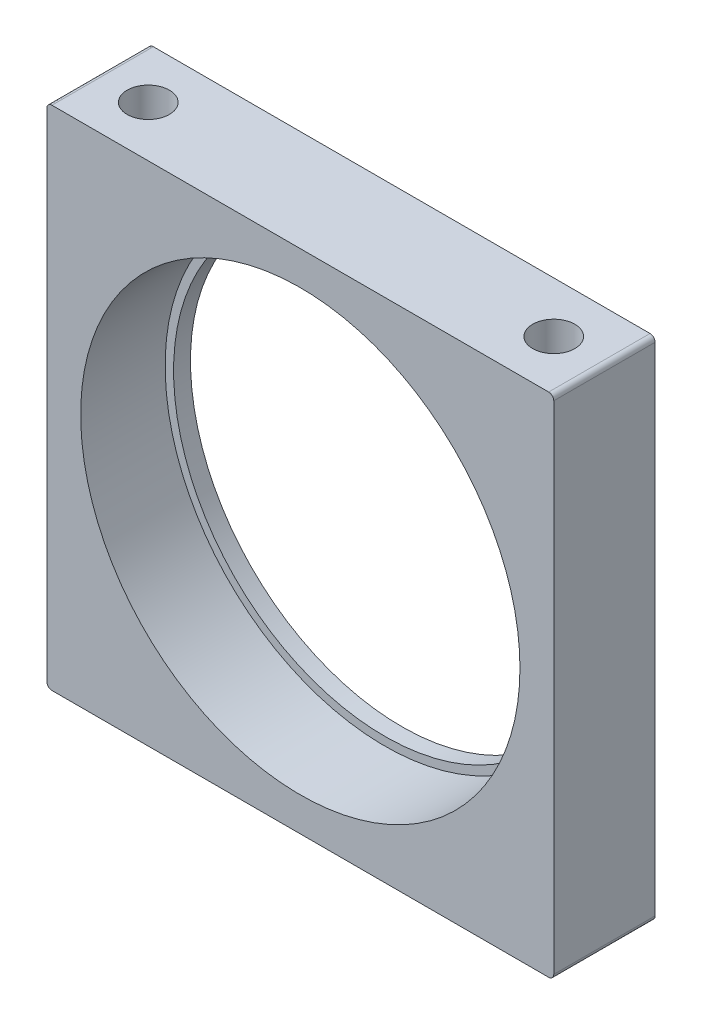
SolidWorks part; units mm, degrees
material "Alliage 1060"
ref_plane "Plan de face" through (0, 0, 0) normal (0, 0, 1) x (1, 0, 0)
ref_plane "Plan de dessus" through (0, 0, 0) normal (0, 1, 0) x (1, 0, 0)
ref_plane "Plan de droite" through (0, 0, 0) normal (1, 0, 0) x (0, 0, -1)
sketch "Esquisse1" plane through (0, 0, 0) normal (0, 0, 1) x (1, 0, 0)
  line L1 (0, 0) -> (30, 0)
  line L2 (0, 0) -> (0, 30)
  line L3 (0, 30) -> (30, 30)
  line L4 (30, 0) -> (30, 30)
  circle A0 centre (15, 15) radius 12.5
  dimension "D3" = 25
  dimension "D1" = 30
  dimension "D2" = 30
  dimension "D4" = 15
  dimension "D5" = 15
extrude "Boss.-Extru.1" add sketch "Esquisse1" along normal blind 6
sketch "Esquisse3" plane through (0, 0, 6) normal (0, 0, 1) x (1, 0, 0)
  line L0 (0, 30) -> (0, 0) construction
  line L2 (0, 0) -> (30, 0) construction
  circle A0 centre (15, 15) radius 13
  dimension "D3" = 26
  dimension "D1" = 15
  dimension "D2" = 15
extrude "Enlèv. mat.-Extru.1" cut sketch "Esquisse3" against normal blind 5
hole_wizard "Trou pour taraudage pour trou taraudé M31" positions "Esquisse6" profile "Esquisse7" hole size "M3" standard "ISO"
sketch "Esquisse6" plane through (0, 30, 0) normal (0, 1, 0) x (1, 0, 0)
  line L0 (0, -6) -> (0, 0) construction
  line L1 (30, -6) -> (30, 0) construction
  line L2 (30, 0) -> (0, 0) construction
  point P0 (3, -3)
  point P2 (27, -3)
  dimension "D1" = 3
  dimension "D2" = 3
  dimension "D3" = 3
  dimension "D4" = 3
sketch "Esquisse7" plane through (3, 30, 3) normal (1, 0, 0) x (0, 0, 1)
  line L0 (0, 0) -> (0, 6.7511)
  line L1 (0, 6.7511) -> (1.25, 6)
  line L2 (1.25, 6) -> (1.25, 0)
  line L5 (1.25, 0) -> (0, 0)
  line L10 (0, 6.7511) -> (-1.25, 6) construction
  line L11 (0, -6.35) -> (0, 107.95) construction
  dimension "Diamètre du perçage" = 2.5
  dimension "Profondeur du perçage" = 6
  dimension "Angle de pointe" = 118
hole_wizard "Trou pour taraudage pour trou taraudé M32" positions "Esquisse8" profile "Esquisse9" hole size "M3" standard "ISO"
sketch "Esquisse8" plane through (0, 0, 0) normal (0, -1, 0) x (-1, 0, 0)
  line L0 (-30, -6) -> (-30, 0) construction
  line L1 (0, -6) -> (0, 0) construction
  line L4 (0, -6) -> (-30, -6) construction
  point P0 (-3, -3)
  point P2 (-27, -3)
  dimension "D1" = 3
  dimension "D2" = 3
  dimension "D3" = 3
  dimension "D4" = 3
sketch "Esquisse9" plane through (3, 0, 3) normal (1, 0, 0) x (0, 0, -1)
  line L0 (0, 0) -> (0, 6.7511)
  line L1 (0, 6.7511) -> (1.25, 6)
  line L2 (1.25, 6) -> (1.25, 0)
  line L5 (1.25, 0) -> (0, 0)
  line L10 (0, 6.7511) -> (-1.25, 6) construction
  line L11 (0, -6.35) -> (0, 107.95) construction
  dimension "Diamètre du perçage" = 2.5
  dimension "Profondeur du perçage" = 6
  dimension "Angle de pointe" = 118
fillet "Congé1" radius 0.3 4 edges at (0, 0, 3) (30, 0, 3) (0, 30, 3) (30, 30, 3)
equation "\"D4@Esquisse1\"=\"D2@Esquisse1\"/2"
equation "\"D5@Esquisse1\"=\"D2@Esquisse1\"/2"
